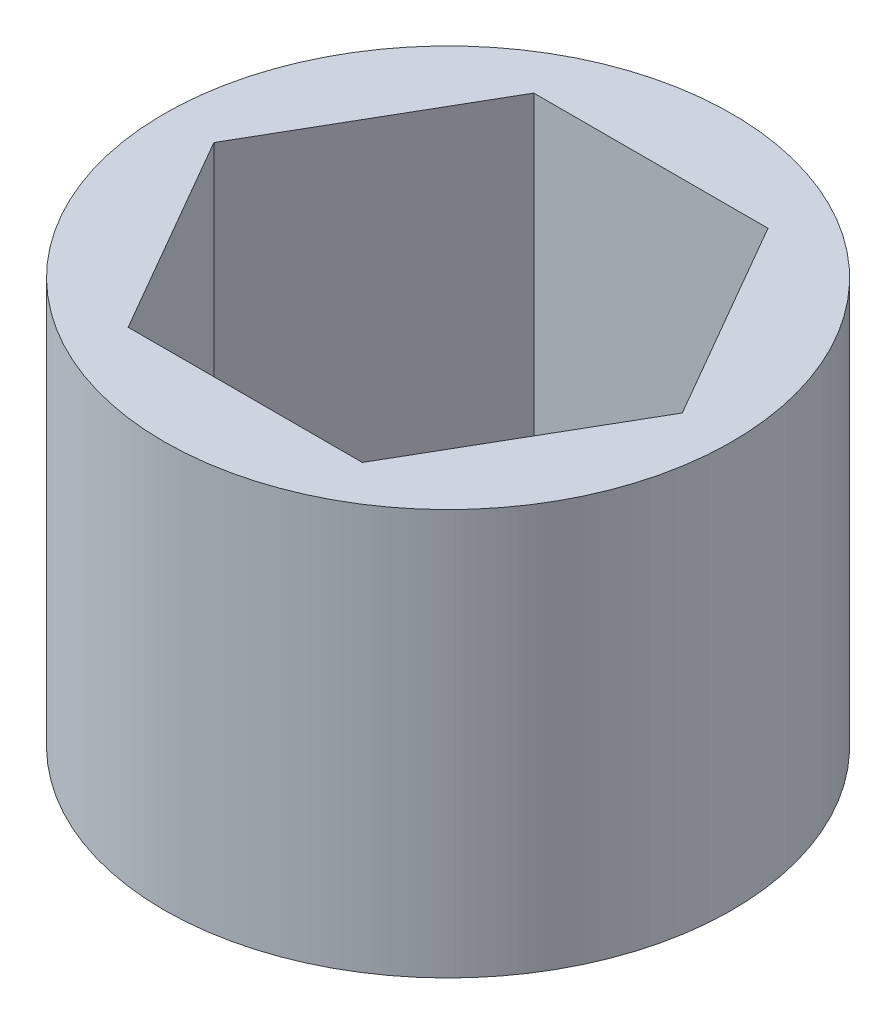
SolidWorks part; units mm, degrees
ref_plane "Front Plane" through (0, 0, 0) normal (0, 0, 1) x (1, 0, 0)
ref_plane "Top Plane" through (0, 0, 0) normal (0, 1, 0) x (1, 0, 0)
ref_plane "Right Plane" through (0, 0, 0) normal (1, 0, 0) x (0, 0, -1)
sketch "Sketch1" plane through (0, 0, 0) normal (0, 1, 0) x (1, 0, 0)
  line L1 (7.3323, 0) -> (3.6662, 6.35)
  line L2 (3.6662, 6.35) -> (-3.6662, 6.35)
  line L3 (-3.6662, 6.35) -> (-7.3323, 0)
  line L4 (-7.3323, 0) -> (-3.6662, -6.35)
  line L5 (-3.6662, -6.35) -> (3.6662, -6.35)
  line L6 (3.6662, -6.35) -> (7.3323, 0)
  circle A0 centre (0, 0) radius 6.35 construction
  circle A1 centre (0, 0) radius 8.89
  dimension "D1" = 12.7
  dimension "D3" = 17.78
  dimension "D2" = 6.35
extrude "Boss-Extrude1" add sketch "Sketch1" along normal blind 12.7
